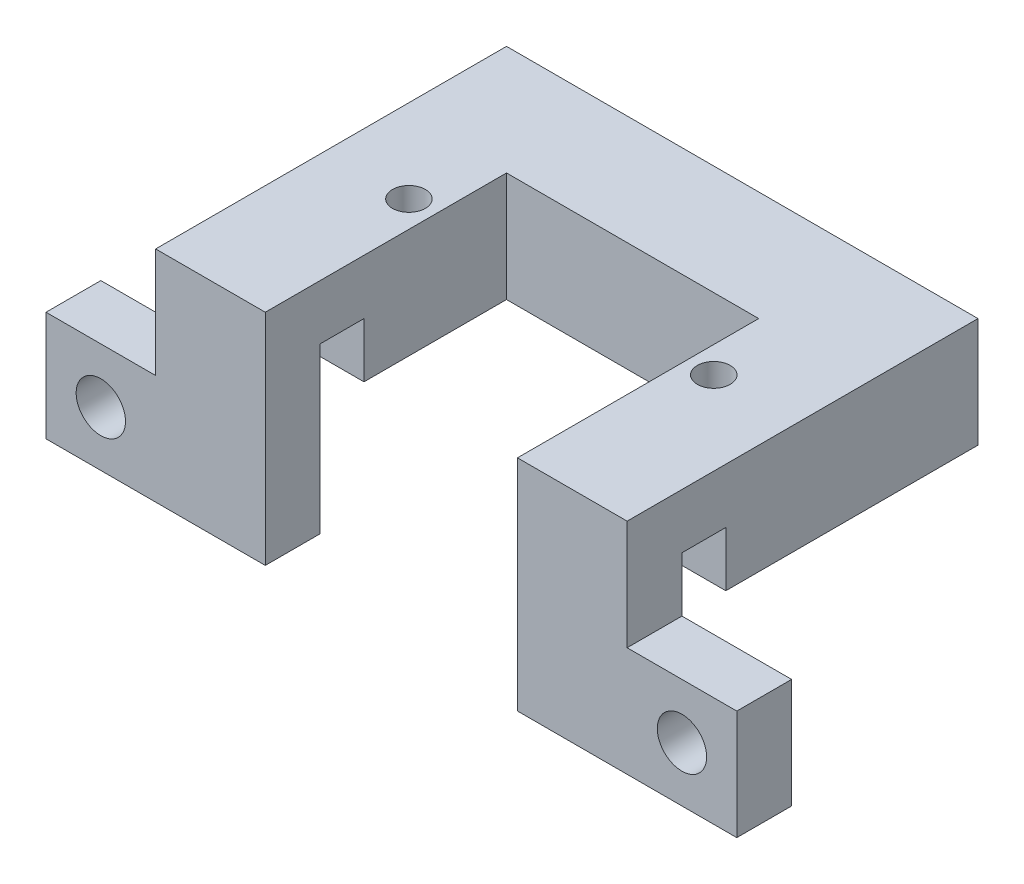
SolidWorks part; units mm, degrees
ref_plane "Plano frontal" through (0, 0, 0) normal (0, 0, 1) x (1, 0, 0)
ref_plane "Plano superior" through (0, 0, 0) normal (0, 1, 0) x (1, 0, 0)
ref_plane "Plano direito" through (0, 0, 0) normal (1, 0, 0) x (0, 0, -1)
sketch "Esboço1" plane through (0, 0, 0) normal (0, 1, 0) x (1, 0, 0)
  line L0 (-21.5, 0) -> (-21.5, -23)
  line L1 (-21.5, -23) -> (-11.5, -23)
  line L2 (-11.5, -23) -> (-11.5, -10)
  line L3 (-11.5, -10) -> (11.5, -10)
  line L4 (11.5, -10) -> (11.5, -23)
  line L5 (11.5, -23) -> (21.5, -23)
  line L6 (21.5, -23) -> (21.5, 0)
  line L7 (21.5, 0) -> (-21.5, 0)
  point P2 (0, 0)
  dimension "D1" = 10
  dimension "D2" = 10
  dimension "D3" = 10
  dimension "D4" = 23
  dimension "D5" = 13
  dimension "D6" = 13
extrude "Ressalto-extrusão1" add sketch "Esboço1" along normal blind 10
sketch "Esboço2" plane through (0, 10, 0) normal (0, 1, 0) x (1, 0, 0)
  line L0 (-11.5, -23) -> (-11.5, -10) construction
  line L1 (11.5, -10) -> (11.5, -23) construction
  line L2 (-21.5, -23) -> (-11.5, -23) construction
  line L3 (11.5, -23) -> (21.5, -23) construction
  circle A0 centre (-13.9, -16.5) radius 1.5
  circle A1 centre (13.9, -16.5) radius 1.5
  dimension "D1" = 3
  dimension "D2" = 3
  dimension "D3" = 2.4
  dimension "D4" = 2.4
  dimension "D5" = 6.5
  dimension "D6" = 6.5
extrude "Corte-extrusão1" cut sketch "Esboço2" against normal through all
sketch "Esboço3" plane through (0, 10, 0) normal (0, 1, 0) x (1, 0, 0)
  line L0 (-21.5, -23) -> (-21.5, -27)
  line L1 (-21.5, -27) -> (-21.5, -32)
  line L2 (-11.5, -23) -> (-11.5, -27)
  line L3 (-11.5, -27) -> (-11.5, -32)
  line L4 (-11.5, -32) -> (-21.5, -32)
  line L5 (-21.5, -23) -> (-11.5, -23)
  line L6 (11.5, -23) -> (21.5, -23)
  line L7 (21.5, -23) -> (21.5, -27)
  line L8 (21.5, -27) -> (21.5, -32)
  line L9 (11.5, -23) -> (11.5, -27)
  line L10 (11.5, -27) -> (11.5, -32)
  line L11 (11.5, -32) -> (21.5, -32)
  dimension "D1" = 4
  dimension "D2" = 4
  dimension "D3" = 5
  dimension "D4" = 4
  dimension "D5" = 4
  dimension "D6" = 5
extrude "Ressalto-extrusão2" add sketch "Esboço3" against normal blind 10
sketch "Esboço4" plane through (21.5, 0, 0) normal (1, 0, 0) x (0, 0, -1)
  line L0 (-32, 5) -> (-27, 5) construction
  line L4 (-32, 0) -> (0, 0) construction
  line L5 (-23, 0) -> (-27, 0)
  line L6 (-27, 0) -> (-27, 5)
  line L8 (-27, 5) -> (-23, 5)
  line L9 (-23, 5) -> (-23, 0)
  line L10 (-32, 0) -> (-32, 10) construction
  dimension "D1" = 5
  dimension "D2" = 4
  dimension "D3" = 5
extrude "Corte-extrusão4" cut sketch "Esboço4" against normal through all
sketch "Esboço5" plane through (0, 0, 0) normal (0, -1, 0) x (1, 0, 0)
  line L1 (-21.5, 32) -> (-11.5, 32)
  line L2 (-21.5, 32) -> (-21.5, 27)
  line L3 (-21.5, 27) -> (-11.5, 27)
  line L4 (-11.5, 32) -> (-11.5, 27)
  line L5 (11.5, 32) -> (21.5, 32)
  line L6 (11.5, 32) -> (11.5, 27)
  line L7 (11.5, 27) -> (21.5, 27)
  line L8 (21.5, 32) -> (21.5, 27)
extrude "Ressalto-extrusão3" add sketch "Esboço5" along normal blind 10
sketch "Esboço6" plane through (0, 0, 32) normal (0, 0, 1) x (1, 0, 0)
  line L1 (-21.5, -10) -> (-31.5, -10)
  line L2 (-21.5, -10) -> (-21.5, 0)
  line L3 (-21.5, 0) -> (-31.5, 0)
  line L4 (-31.5, -10) -> (-31.5, 0)
  line L5 (21.5, -10) -> (31.5, -10)
  line L6 (21.5, -10) -> (21.5, 0)
  line L7 (21.5, 0) -> (31.5, 0)
  line L8 (31.5, -10) -> (31.5, 0)
  dimension "D1" = 10
  dimension "D2" = 10
  dimension "D3" = 10
  dimension "D4" = 10
extrude "Ressalto-extrusão4" add sketch "Esboço6" against normal blind 5
hole_wizard "Furo com folga de M41" positions "3DSketch1" profile "Esboço8" hole size "M4" standard "ISO" end condition through all
sketch3d "3DSketch1"
  line L0 (-26.5, 0, 32) -> (-26.5, -5, 32) construction
  line L1 (-21.5, 0, 32) -> (-31.5, 0, 32) construction
  line L3 (-31.5, -5, 32) -> (-26.5, -5, 32) construction
  line L4 (-31.5, 0, 32) -> (-31.5, -10, 32) construction
  line L6 (26.5, 0, 32) -> (26.5, -5, 32) construction
  line L7 (31.5, 0, 32) -> (21.5, 0, 32) construction
  line L9 (31.5, -5, 32) -> (26.5, -5, 32) construction
  line L10 (31.5, -10, 32) -> (31.5, 0, 32) construction
  point P0 (-26.5, -5, 32)
  point P2 (26.5, -5, 32)
  point P30 (0, 0, 0)
  point P31 (26.5, -5, 32)
sketch "Esboço8" plane through (-26.5, -5, 32) normal (1, 0, 0) x (0, -1, 0)
  line L0 (0, 0) -> (0, 32)
  line L1 (0, 32) -> (2.25, 32)
  line L2 (2.25, 32) -> (2.25, 0)
  line L5 (2.25, 0) -> (0, 0)
  line L11 (0, -6.35) -> (0, 107.95) construction
  dimension "Thru Hole Dia." = 4.5
  dimension "Thru Hole Depth" = 32
